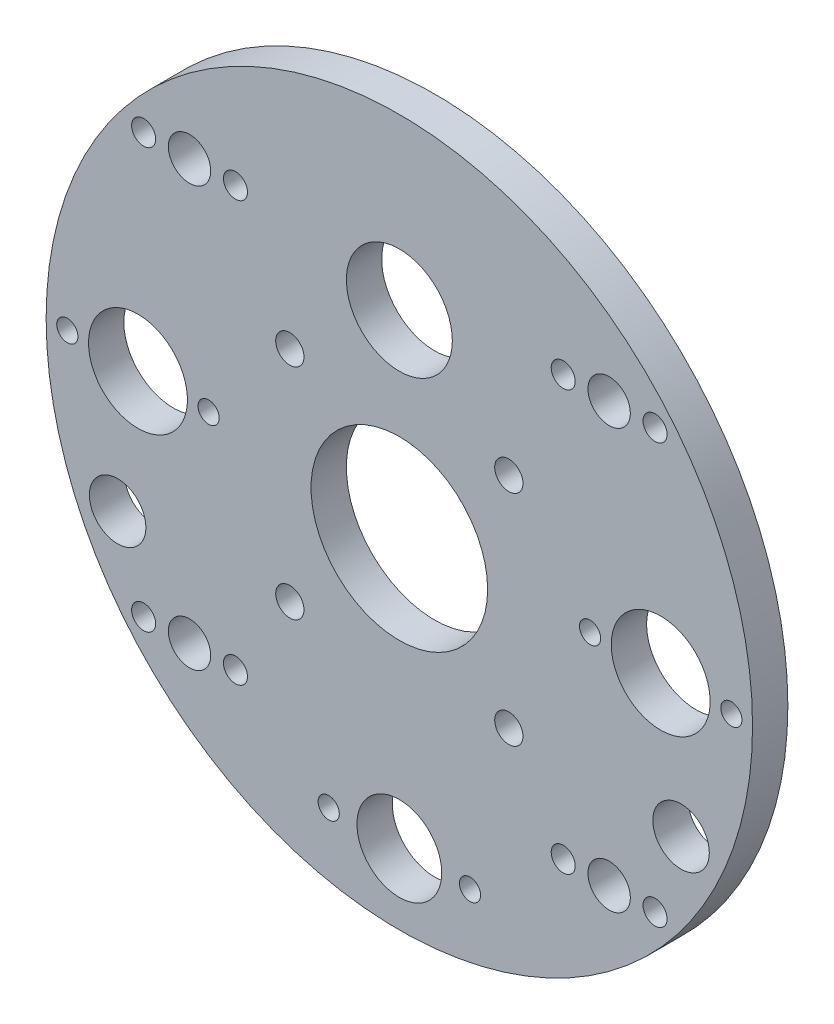
SolidWorks part; units mm, degrees
material "Acrylic (Medium-high impact)"
ref_plane "Front Plane" through (0, 0, 0) normal (0, 0, 1) x (1, 0, 0)
ref_plane "Top Plane" through (0, 0, 0) normal (0, 1, 0) x (1, 0, 0)
ref_plane "Right Plane" through (0, 0, 0) normal (1, 0, 0) x (0, 0, -1)
sketch "Sketch1" plane through (0, 0, 0) normal (0, 0, 1) x (1, 0, 0)
  circle A0 centre (0, 0) radius 50
  dimension "D1" = 100
extrude "Boss-Extrude1" add sketch "Sketch1" along normal blind 5
hole_wizard "Ø14.0 (14) Diameter Hole1" positions "Sketch5" profile "Sketch6" hole size "Ø14.0" standard "ISO"
sketch "Sketch5" plane through (0, 0, 0) normal (0, 0, -1) x (-1, 0, 0)
  point P4 (37, 0)
  point P17 (-37, 0)
  point P21 (0, -37) [skipped]
  dimension "D1" = 3
  dimension "D3" = 37
sketch "Sketch6" plane through (-37, 0, 0) normal (1, 0, 0) x (0, 1, 0)
  line L0 (0, 0) -> (0, 5)
  line L1 (0, 5) -> (7, 5)
  line L2 (7, 5) -> (7, 0)
  line L5 (7, 0) -> (0, 0)
  line L11 (0, -6.35) -> (0, 107.95) construction
  dimension "Thru Hole Dia." = 14
  dimension "Thru Hole Depth" = 5
sketch "Sketch9" plane through (0, 0, 5) normal (0, 0, 1) x (1, 0, 0)
  circle A0 centre (0, 26) radius 7.5
  dimension "D1" = 15
  dimension "D2" = 26
extrude "Cut-Extrude1" cut sketch "Sketch9" against normal blind 10 contours A0
sketch "Sketch10" plane through (0, 0, 5) normal (0, 0, 1) x (1, 0, 0)
  circle A0 centre (0, -2) radius 12.5
  circle A1 centre (-15.5, 13.5) radius 2
  circle A8 centre (15.5, 13.5) radius 2
  circle A9 centre (15.5, -17.5) radius 2
  circle A10 centre (-15.5, -17.5) radius 2
  point P14 (0, -2)
  dimension "D1" = 4
  dimension "D2" = 25
  dimension "D3" = 15.5
  dimension "D4" = 15.5
  dimension "D6" = 2
  dimension "D5" = 4
extrude "Cut-Extrude2" cut sketch "Sketch10" against normal blind 10
sketch "Sketch11" plane through (0, 0, 5) normal (0, 0, 1) x (1, 0, 0)
  line L0 (0, 0) -> (-37, 0) construction
  line L1 (0, 0) -> (-29.6985, 29.6985) construction
  circle A0 centre (-29.6985, 29.6985) radius 3
  dimension "D3" = 6
  dimension "D1" = 45
  dimension "D2" = 42
extrude "Cut-Extrude3" cut sketch "Sketch11" against normal blind 10
pattern_circular "CirPattern1" count 4 over 360 about axis through (0, 0, 0) along (0, 0, 1) of "Cut-Extrude3"
sketch "Sketch12" plane through (0, 0, 5) normal (0, 0, 1) x (1, 0, 0)
  circle A0 centre (-47, 0) radius 1.5
  circle A1 centre (-27, 0) radius 1.5
  circle A2 centre (27, 0) radius 1.5
  circle A3 centre (47, 0) radius 1.5
  circle A4 centre (-10, -40) radius 1.5
  circle A5 centre (10, -40) radius 1.5
  circle A7 centre (37, 0) radius 7 construction
  circle A8 centre (0, -40) radius 6
  circle A9 centre (-37, 0) radius 7 construction
  dimension "D1" = 3
  dimension "D2" = 3
  dimension "D3" = 3
  dimension "D4" = 3
  dimension "D5" = 3
  dimension "D6" = 3
  dimension "D7" = 10
  dimension "D8" = 10
  dimension "D9" = 10
  dimension "D10" = 10
  dimension "D11" = 10
  dimension "D12" = 10
  dimension "D13" = 40
  dimension "D15" = 12
  dimension "D16" = 40
  dimension "D14" = 40
extrude "Cut-Extrude4" cut sketch "Sketch12" against normal blind 10
sketch "Sketch13" plane through (0, 0, 5) normal (0, 0, 1) x (1, 0, 0)
  line L0 (0, 0) -> (-39.8775, -18.5952) construction
  line L1 (0, 0) -> (0, -19.8721) construction
  circle A0 centre (-39.8775, -18.5952) radius 4
  circle A1 centre (39.8775, -18.5952) radius 4
  dimension "D1" = 8
  dimension "D2" = 44
  dimension "D3" = 65
extrude "Cut-Extrude5" cut sketch "Sketch13" against normal blind 10
hole_wizard "M3 Clearance Hole1" positions "Sketch14" profile "Sketch15" hole size "M3" standard "ISO" end condition through all
sketch "Sketch14" plane through (0, 0, 5) normal (0, 0, 1) x (1, 0, 0)
  circle A1 centre (-29.6985, -29.6985) radius 3 construction
  point P0 (-36.1985, -29.6985)
  point P2 (-23.1985, -29.6985)
  dimension "D1" = 6
  dimension "D2" = 13
  dimension "D3" = 6.5
sketch "Sketch15" plane through (-36.1985, -29.6985, 5) normal (1, 0, 0) x (0, -1, 0)
  line L0 (0, 0) -> (0, 5)
  line L1 (0, 5) -> (1.7, 5)
  line L2 (1.7, 5) -> (1.7, 0)
  line L5 (1.7, 0) -> (0, 0)
  line L11 (0, -6.35) -> (0, 107.95) construction
  dimension "Thru Hole Dia." = 3.4
  dimension "Thru Hole Depth" = 5
mirror "Mirror1" about plane through (0, 0, 0) normal (0, 1, 0) of "M3 Clearance Hole1"
mirror "Mirror2" about plane through (0, 0, 0) normal (1, 0, 0) of "Mirror1", "M3 Clearance Hole1"
